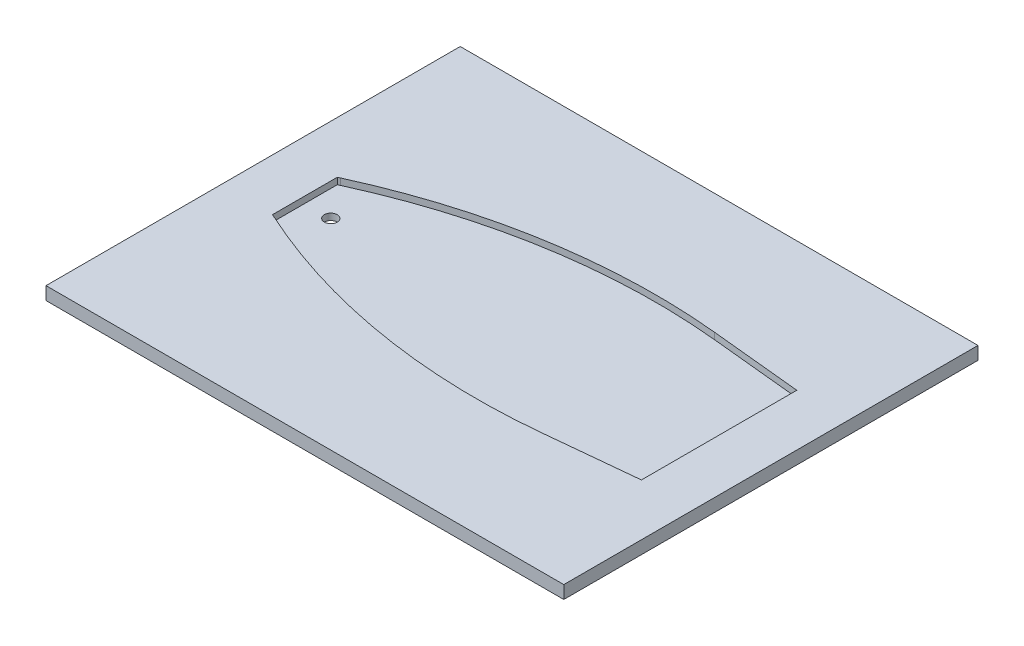
SolidWorks part; units mm, degrees
ref_plane "Front Plane" through (0, 0, 0) normal (0, 0, 1) x (1, 0, 0)
ref_plane "Top Plane" through (0, 0, 0) normal (0, 1, 0) x (1, 0, 0)
ref_plane "Right Plane" through (0, 0, 0) normal (1, 0, 0) x (0, 0, -1)
sketch "Sketch1" plane through (0, 0, 0) normal (0, 1, 0) x (1, 0, 0)
  line L1 (-127, 101.6) -> (127, 101.6)
  line L2 (-127, 101.6) -> (-127, -101.6)
  line L3 (-127, -101.6) -> (127, -101.6)
  line L4 (127, 101.6) -> (127, -101.6)
  line L5 (-127, 101.6) -> (127, -101.6) construction
  line L6 (-127, -101.6) -> (127, 101.6) construction
  point P0 (0, 0)
  dimension "D1" = 254
  dimension "D2" = 203.2
extrude "Boss-Extrude1" add sketch "Sketch1" along normal blind 6.35
sketch "Sketch2" plane through (0, 6.35, 0) normal (0, 1, 0) x (1, 0, 0)
  line L0 (-127, 101.6) -> (-127, -101.6) construction
  circle A0 centre (-88.9, 0) radius 3.175
  dimension "D1" = 6.35
  dimension "D2" = 38.1
extrude "Cut-Extrude1" cut sketch "Sketch2" against normal blind 6.35
sketch "Sketch5" plane through (0, 6.35, 0) normal (0, 1, 0) x (1, 0, 0)
  line L0 (-101.6, 15.875) -> (-101.6, -15.875)
  line L1 (-101.6, -15.875) -> (-25.4, -50.8)
  line L2 (-25.4, -50.8) -> (101.6, -38.1)
  line L3 (101.6, -38.1) -> (101.6, 38.1)
  line L4 (101.6, 38.1) -> (-25.4, 50.8)
  line L5 (-25.4, 50.8) -> (-101.6, 15.875)
  line L6 (127, -101.6) -> (127, 101.6) construction
  point P8 (-101.6, 0)
  point P13 (101.6, 0)
  dimension "D1" = 31.75
  dimension "D2" = 76.2
  dimension "D3" = 203.2
  dimension "D4" = 25.4
  dimension "D5" = 76.2
  dimension "D6" = 76.2
  dimension "D7" = 101.6
extrude "Cut-Extrude3" cut sketch "Sketch5" against normal blind 3.175
fillet "Fillet2" radius 304.8 2 edges at (-25.4, 4.7625, 50.8) (-25.4, 4.7625, -50.8)
sketch "Sketch9" plane through (0, 6.35, 0) normal (0, 1, 0) x (1, 0, 0)
  circle A0 centre (-88.9, 0) radius 76.2
  circle A1 centre (-88.9, 0) radius 71.12
  arc A2 (-12.7, 0) -> (-88.9, 76.2) centre (-88.9, 0) ccw
  arc A3 (-88.9, 80.3923) -> (-8.5077, 0) centre (-88.9, 0) cw
  arc A4 (-8.5077, 0) -> (-88.9, -80.3923) centre (-88.9, 0) cw
  dimension "D1" = 152.4
  dimension "D2" = 142.24
sketch "Sketch10" plane through (0, 3.175, 0) normal (0, 1, 0) x (1, 0, 0)
  line L0 (-12.7, 0) -> (-17.78, 0)
  line L1 (-12.99, -6.6413) -> (-18.0506, -6.1985)
  line L2 (-13.8576, -13.232) -> (-18.8605, -12.3499)
  line L3 (-15.2965, -19.722) -> (-20.2034, -18.4072)
  line L4 (-17.2954, -26.0619) -> (-22.0691, -24.3245)
  line L5 (-19.8393, -32.2035) -> (-24.4434, -30.0566)
  line L6 (-22.9089, -38.1) -> (-27.3083, -35.56)
  line L7 (-26.4806, -43.7065) -> (-30.6419, -40.7928)
  line L8 (-30.5274, -48.9804) -> (-34.4189, -45.7151)
  line L9 (-35.0185, -53.8815) -> (-38.6106, -50.2894)
  line L10 (-39.9196, -58.3726) -> (-43.1849, -54.4811)
  line L11 (-45.1935, -62.4194) -> (-48.1072, -58.2581)
  line L12 (-50.8, -65.9911) -> (-53.34, -61.5917)
  line L13 (-56.6965, -69.0607) -> (-58.8434, -64.4566)
  line L14 (-62.8381, -71.6046) -> (-64.5755, -66.8309)
  line L15 (-69.178, -73.6035) -> (-70.4928, -68.6966)
  line L16 (-75.668, -75.0424) -> (-76.5501, -70.0395)
  line L17 (-82.2587, -75.91) -> (-82.7015, -70.8494)
  line L18 (-88.9, -76.2) -> (-88.9, -71.12)
  line L19 (-88.9, 0) -> (-17.78, 0) construction
  line L20 (-88.9, 0) -> (-18.0506, -6.1985) construction
  line L21 (-12.99, 6.6413) -> (-18.0506, 6.1985)
  line L22 (-13.8576, 13.232) -> (-18.8605, 12.3499)
  line L23 (-15.2965, 19.722) -> (-20.2034, 18.4072)
  line L24 (-17.2954, 26.0619) -> (-22.0691, 24.3245)
  line L25 (-19.8393, 32.2035) -> (-24.4434, 30.0566)
  line L26 (-22.9089, 38.1) -> (-27.3083, 35.56)
  line L27 (-26.4806, 43.7065) -> (-30.6419, 40.7928)
  line L28 (-30.5274, 48.9804) -> (-34.4189, 45.7151)
  line L29 (-35.0185, 53.8815) -> (-38.6106, 50.2894)
  line L30 (-39.9196, 58.3726) -> (-43.1849, 54.4811)
  line L31 (-45.1935, 62.4194) -> (-48.1072, 58.2581)
  line L32 (-50.8, 65.9911) -> (-53.34, 61.5917)
  line L33 (-56.6965, 69.0607) -> (-58.8434, 64.4566)
  line L34 (-62.8381, 71.6046) -> (-64.5755, 66.8309)
  line L35 (-69.178, 73.6035) -> (-70.4928, 68.6966)
  line L36 (-75.668, 75.0424) -> (-76.5501, 70.0395)
  line L37 (-82.2587, 75.91) -> (-82.7015, 70.8494)
  line L38 (-88.9, 76.2) -> (-88.9, 71.12)
  line L39 (-88.9, 0) -> (-17.78, 0) construction
  line L40 (-88.9, 0) -> (-18.0506, 6.1985) construction
  circle A0 centre (-88.9, 0) radius 76.2 construction
  circle A1 centre (-88.9, 0) radius 71.12 construction
  text T0 "90     80      70      60       50      40       30      20      10        0"
  text T1 "        10       20      30       40       50      60      70      80      90"
  dimension "D2" = 5
  dimension "D4" = 5
  dimension "D1" = 19
  dimension "D3" = 19
